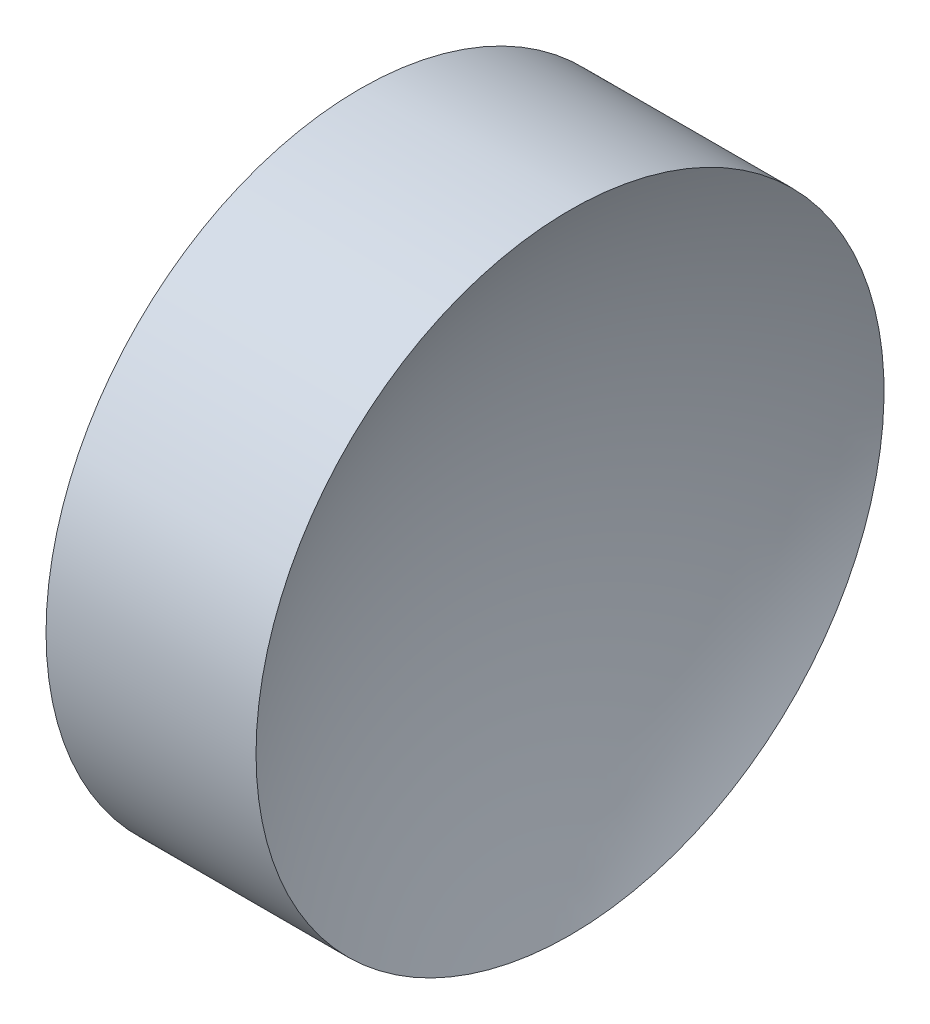
SolidWorks part; units mm, degrees
ref_plane "前视基准面" through (0, 0, 0) normal (0, 0, 1) x (1, 0, 0)
ref_plane "上视基准面" through (0, 0, 0) normal (0, 1, 0) x (1, 0, 0)
ref_plane "右视基准面" through (0, 0, 0) normal (1, 0, 0) x (0, 0, -1)
sketch "草图1" plane through (0, 0, 0) normal (0, 0, 1) x (1, 0, 0)
  line L0 (53.0623, 32.6113) -> (69.5807, 32.6113) construction
  line L1 (61.0525, 32.6113) -> (59.0525, 32.6113)
  line L3 (60.0525, 45.1113) -> (64.2322, 45.1113)
  line L4 (60.0525, 45.1113) -> (55.8728, 45.1113)
  arc A0 (64.2322, 45.1113) -> (61.0525, 32.6113) centre (87.2125, 32.6113) ccw
  arc A1 (59.0525, 32.6113) -> (55.8728, 45.1113) centre (32.8925, 32.6113) ccw
revolve "旋转1" add sketch "草图1" angle 360 about L0
